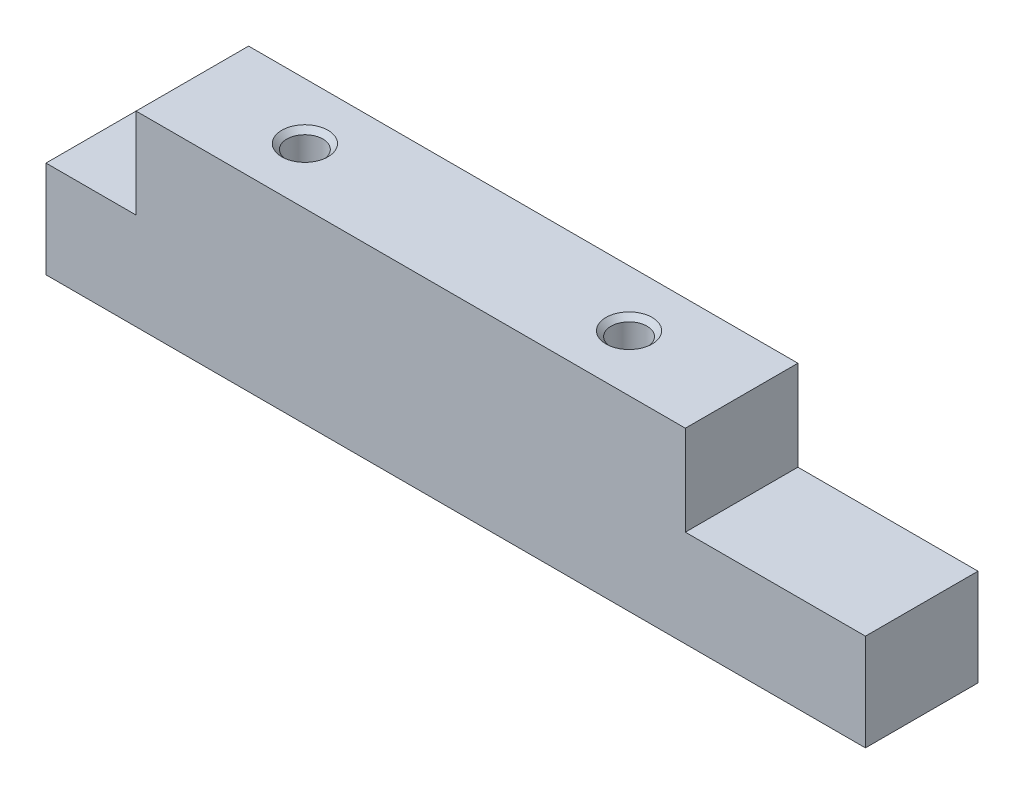
SolidWorks part; units mm, degrees
ref_plane "Front Plane" through (0, 0, 0) normal (0, 0, 1) x (1, 0, 0)
ref_plane "Top Plane" through (0, 0, 0) normal (0, 1, 0) x (1, 0, 0)
ref_plane "Right Plane" through (0, 0, 0) normal (1, 0, 0) x (0, 0, -1)
sketch "Sketch2" plane through (0, 0, 0) normal (0, 1, 0) x (1, 0, 0)
  line L1 (0, 0) -> (36.4, 0)
  line L2 (0, 0) -> (0, 5)
  line L3 (0, 5) -> (36.4, 5)
  line L4 (36.4, 0) -> (36.4, 5)
  dimension "D1" = 36.4
  dimension "D2" = 5
extrude "Boss-Extrude1" add sketch "Sketch2" along normal blind 4.3
sketch "Sketch3" plane through (0, 4.3, 0) normal (0, 1, 0) x (1, 0, 0)
  line L0 (0, 0) -> (36.4, 0) construction
  line L1 (4, 0) -> (28.4, 0)
  line L2 (4, 0) -> (4, 5)
  line L3 (4, 5) -> (28.4, 5)
  line L4 (28.4, 0) -> (28.4, 5)
  line L5 (36.4, 5) -> (0, 5) construction
  line L6 (0, 5) -> (0, 0) construction
  line L7 (36.4, 0) -> (36.4, 5) construction
  dimension "D1" = 4
  dimension "D2" = 8
extrude "Boss-Extrude2" add sketch "Sketch3" along normal blind 4
hole_wizard "M2x0.4 Tapped Hole1" positions "Sketch5" profile "Sketch4" tap size "M2x0.4" standard "ANSI Metric"
sketch "Sketch5" plane through (0, 8.3, 0) normal (0, 1, 0) x (1, 0, 0)
  line L0 (0, 5) -> (0, 0) construction
  line L1 (36.4, 0) -> (36.4, 5) construction
  line L2 (4, 0) -> (28.4, 0) construction
  point P0 (9, 2.5)
  point P2 (23.4, 2.5)
  dimension "D1" = 9
  dimension "D2" = 13
  dimension "D3" = 2.5
  dimension "D4" = 2.5
sketch "Sketch4" plane through (9, 8.3, -2.5) normal (1, 0, 0) x (0, 0, 1)
  line L0 (0, 0) -> (0, 5.4807)
  line L1 (0, 5.4807) -> (0.8, 5)
  line L2 (0.8, 5) -> (0.8, 0.225)
  line L3 (0.8, 0.225) -> (1.025, 0)
  line L5 (1.025, 0) -> (0, 0)
  line L6 (-0.8, 0.225) -> (-1.025, 0) construction
  line L10 (0, 5.4807) -> (-0.8, 5) construction
  line L11 (0, -6.35) -> (0, 107.95) construction
  dimension "Tap Drill Dia." = 1.6
  dimension "Tap Drill Depth" = 5
  dimension "Near C'Sink Dia." = 2.05
  dimension "Near C'Sink Angle" = 90
  dimension "Drill Angle" = 118
cosmetic thread "Hole Thread1" parameters "D1"=5, "D2"=2
cosmetic thread "Hole Thread2" parameters "D1"=5, "D2"=2
